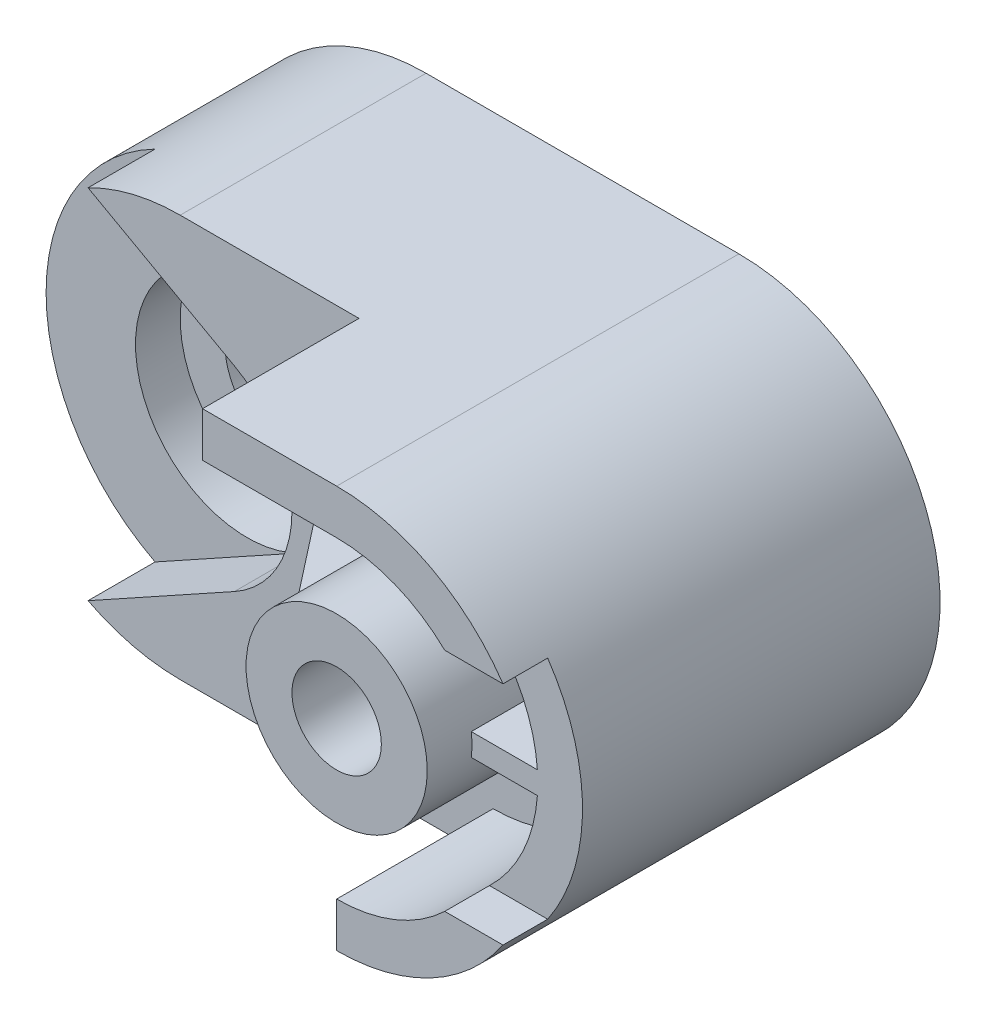
SolidWorks part; units mm, degrees
ref_plane "Front Plane" through (0, 0, 0) normal (0, 0, 1) x (1, 0, 0)
ref_plane "Top Plane" through (0, 0, 0) normal (0, 1, 0) x (1, 0, 0)
ref_plane "Right Plane" through (0, 0, 0) normal (1, 0, 0) x (0, 0, -1)
sketch "Sketch1" plane through (0, 0, 0) normal (0, 0, 1) x (1, 0, 0)
  line L0 (0, 0) -> (70, 0) construction
  line L1 (0, 45) -> (70, 45)
  line L2 (0, -45) -> (70, -45)
  arc A0 (0, 45) -> (0, -45) centre (0, 0) ccw
  arc A1 (70, -45) -> (70, 45) centre (70, 0) ccw
  point P3 (35, 0)
  dimension "D2" = 45
  dimension "D1" = 70
extrude "Boss-Extrude1" add sketch "Sketch1" along normal blind 90
sketch "Sketch2" plane through (0, 0, 0) normal (0, 0, -1) x (-1, 0, 0)
  line L0 (0, 0) -> (-70, 0) construction
  line L1 (0, -25) -> (-70, -25)
  line L2 (0, 25) -> (-70, 25)
  arc A0 (0, -25) -> (0, 25) centre (0, 0) ccw
  arc A1 (-70, 25) -> (-70, -25) centre (-70, 0) ccw
  point P4 (-35, 0)
  dimension "D1" = 25
extrude "Cut-Extrude1" cut sketch "Sketch2" against normal blind 10
sketch "Sketch3" plane through (0, 0, 90) normal (0, 0, 1) x (1, 0, 0)
  circle A0 centre (70, 0) radius 10
  dimension "D1" = 20
extrude "Cut-Extrude2" cut sketch "Sketch3" against normal blind 166
sketch "Sketch4" plane through (0, 0, 90) normal (0, 0, 1) x (1, 0, 0)
  line L0 (12.1145, 21.8687) -> (-20.6155, 40)
  line L1 (12.1145, -21.8687) -> (-20.6155, -40)
  circle A0 centre (0, 0) radius 25
  arc A1 (0, 45) -> (0, -45) centre (0, 0) ccw construction
  arc A2 (-20.6155, 40) -> (-20.6155, -40) centre (0, 0) ccw
  arc M2 (0, 45) -> (0, -45) centre (0, 0) ccw
  dimension "D1" = 50
  dimension "D2" = 5
  dimension "D3" = 5
extrude "Cut-Extrude3" cut sketch "Sketch4" against normal blind 50 contours A0 L0 L1 M2 | A0
sketch "Sketch5" plane through (0, 0, 40) normal (0, 0, 1) x (1, 0, 0)
  circle A0 centre (0, 0) radius 25
  dimension "D1" = 50
extrude "Cut-Extrude4" cut sketch "Sketch5" against normal blind 10
sketch "Sketch6" plane through (0, 0, 30) normal (0, 0, 1) x (1, 0, 0)
  circle A0 centre (0, 0) radius 15
  dimension "D1" = 30
extrude "Cut-Extrude5" cut sketch "Sketch6" against normal blind 148
sketch "Sketch7" plane through (0, 0, 90) normal (0, 0, 1) x (1, 0, 0)
  line L0 (0, 45) -> (40, 45)
  line L1 (70, 45) -> (0, 45) construction
  line L2 (40, 45) -> (40, 35)
  line L3 (40, 35) -> (70, 35)
  line L4 (104.641, 5) -> (89.641, 5)
  line L5 (12.1145, 21.8687) -> (-20.6155, 40) construction
  line L6 (-20.6155, 40) -> (12.1145, 21.8687)
  line L7 (12.1145, -21.8687) -> (-20.6155, -40) construction
  line L8 (12.1145, -21.8687) -> (-20.6155, -40)
  line L9 (0, -45) -> (70, -45) construction
  line L10 (0, -45) -> (70, -45)
  line L11 (70, -45) -> (70, -35)
  line L12 (104.641, -5) -> (89.3649, -5)
  arc A0 (0, 45) -> (-20.6155, 40) centre (0, 0) ccw construction
  arc A1 (70, 35) -> (104.641, 5) centre (70, 0) cw
  circle A2 centre (70, 0) radius 20
  arc A3 (0, 45) -> (-20.6155, 40) centre (0, 0) ccw
  arc A4 (12.1145, 21.8687) -> (12.1145, -21.8687) centre (0, 0) cw
  arc A5 (-20.6155, -40) -> (0, -45) centre (0, 0) ccw
  arc A6 (70, -35) -> (104.641, -5) centre (70, 0) ccw
  circle A7 centre (70, 0) radius 20.2674
  arc M2 (12.1145, 21.8687) -> (12.1145, -21.8687) centre (0, 0) cw
  line M3 (12.1145, -21.8687) -> (-20.6155, -40)
  arc M4 (-20.6155, -40) -> (0, -45) centre (0, 0) ccw
  line M5 (0, -45) -> (70, -45)
  line M7 (70, 45) -> (0, 45)
  arc M8 (0, 45) -> (-20.6155, 40) centre (0, 0) ccw
  line M9 (-20.6155, 40) -> (12.1145, 21.8687)
  dimension "D6" = 40
  dimension "D1" = 40
  dimension "D2" = 10
  dimension "D3" = 30
  dimension "D4" = 30
  dimension "D5" = 15
  dimension "D7" = 70
  dimension "D8" = 10
  dimension "D9" = 30
  dimension "D10" = 15.2761
extrude "Cut-Extrude6" cut sketch "Sketch7" against normal blind 35 contours A7 L4 A1 L3 L2 L11 A6 L12 M7 M8 M9 M2 M3 M4 M5
sketch "Sketch8" plane through (0, 0, 0) normal (1, 0, 0) x (0, 0, -1)
  line L0 (-90, 35) -> (-90, 5) construction
  line L1 (-90, 25.3) -> (-80, 25.3)
  line L2 (-90, 25.3) -> (-90, 20.3)
  line L3 (-90, 20.3) -> (-80, 20.3)
  line L4 (-80, 25.3) -> (-80, 20.3)
  line L5 (-90, 20.2674) -> (-90, -20.2674) construction
  line L6 (-90, -25.3) -> (-80, -25.3)
  line L7 (-90, -25.3) -> (-90, -20.3)
  line L8 (-90, -20.3) -> (-80, -20.3)
  line L9 (-80, -25.3) -> (-80, -20.3)
  dimension "D1" = 5
  dimension "D2" = 5
  dimension "D3" = 19.7
  dimension "D4" = 19.7
  dimension "D5" = 5
  dimension "D6" = 10
  dimension "D7" = 10
extrude "Cut-Extrude7" cut sketch "Sketch8" along normal blind 145
sketch "Sketch9" plane through (0, 0, 55) normal (0, 0, 1) x (1, 0, 0)
  line L1 (50.359, 5) -> (30.359, 5)
  line L2 (50.359, 5) -> (50.359, -5)
  line L3 (50.359, -5) -> (30.359, -5)
  line L4 (30.359, 5) -> (30.359, -5)
  line L6 (40, 45) -> (0, 45) construction
  arc A0 (89.641, 5) -> (89.641, -5) centre (70, 0) ccw construction
  dimension "D1" = 10
  dimension "D2" = 40
  dimension "D3" = 40
  dimension "D4" = 20
extrude "Boss-Extrude2" add sketch "Sketch9" along normal blind 25
sketch "Sketch10" plane through (0, 0, 90) normal (0, 0, 1) x (1, 0, 0)
  line L0 (89.641, 5) -> (104.641, 5)
  line L1 (98.5116, 20.3) -> (110.1611, 20.3)
  line L2 (110.1611, -20.3) -> (98.5116, -20.3)
  line L3 (104.641, -5) -> (89.641, -5) construction
  line L4 (89.641, -5) -> (104.641, -5)
  arc A0 (98.5116, 20.3) -> (104.641, 5) centre (70, 0) cw
  arc A1 (104.641, 5) -> (98.5116, 20.3) centre (70, 0) ccw construction
  arc A2 (110.1611, 20.3) -> (110.1611, -20.3) centre (70, 0) cw
  arc A3 (110.1611, -20.3) -> (110.1611, 20.3) centre (70, 0) ccw construction
  arc A4 (98.5116, -20.3) -> (104.641, -5) centre (70, 0) ccw
  arc A5 (89.641, 5) -> (89.641, -5) centre (70, 0) cw
extrude "Cut-Extrude8" cut sketch "Sketch10" against normal blind 10 contours A1 A5 A3 L1 L2 L3 L4 A0
sketch "Sketch11" plane through (0, 0, 80) normal (0, 0, 1) x (1, 0, 0)
  line L1 (30.359, 5) -> (50.359, 5)
  line L2 (30.359, 5) -> (30.359, 2.5)
  line L3 (30.359, 2.5) -> (49.8873, 2.5)
  line L5 (30.359, -5) -> (50.359, -5)
  line L6 (30.359, -5) -> (30.359, -2.5)
  line L7 (30.359, -2.5) -> (49.8873, -2.5)
  arc A0 (50.359, 5) -> (50.359, -5) centre (70, 0) ccw construction
  arc A1 (50.359, 5) -> (49.8873, 2.5) centre (70, 0) ccw
  arc A2 (50.359, -5) -> (49.8873, -2.5) centre (70, 0) cw
  arc M1 (50.359, -5) -> (50.359, 5) centre (70, 0) cw
  line M2 (50.359, 5) -> (30.359, 5)
  line M3 (30.359, 5) -> (30.359, -5)
  line M4 (30.359, -5) -> (50.359, -5)
  dimension "D1" = 2.5
  dimension "D2" = 2.5
  dimension "D3" = 20
  dimension "D4" = 20
extrude "Cut-Extrude9" cut sketch "Sketch11" against normal blind 25 contours L7 M3 M4 M1 | L3 M3 M1 M2
sketch "Sketch12" plane through (0, 0, 80) normal (0, 0, 1) x (1, 0, 0)
  line L0 (89.641, 5) -> (104.641, 5)
  line L1 (90.1127, -2.5) -> (104.9106, -2.5)
  line L2 (90.1127, 2.5) -> (104.9106, 2.5)
  arc A0 (89.641, 5) -> (90.1127, 2.5) centre (70, 0) cw
  arc A1 (89.641, -5) -> (90.1127, -2.5) centre (70, 0) ccw
  arc A2 (104.641, 5) -> (104.9106, 2.5) centre (70, 0) cw
  arc A3 (104.641, -5) -> (104.9106, -2.5) centre (70, 0) ccw
  line M4 (104.641, 5) -> (89.641, 5)
  arc M5 (89.641, 5) -> (89.641, -5) centre (70, 0) cw
  line M6 (89.641, -5) -> (104.641, -5)
  dimension "D1" = 2.5
  dimension "D2" = 2.5
  dimension "D3" = 2.5
  dimension "D4" = 2.5
extrude "Cut-Extrude10" cut sketch "Sketch12" against normal blind 25 contours A3 L1 M6 M5 | A2 L2 M4 M5
sketch "Sketch13" plane through (0, -2.5, 0) normal (0, -1, 0) x (1, 0, 0)
  line L0 (49.8873, 80) -> (30.359, 55)
  line L1 (30.359, 55) -> (30.359, 80)
  line L2 (30.359, 80) -> (49.8873, 80)
extrude "Cut-Extrude11" cut sketch "Sketch13" against normal blind 10
equation "\"cm\"=25"
